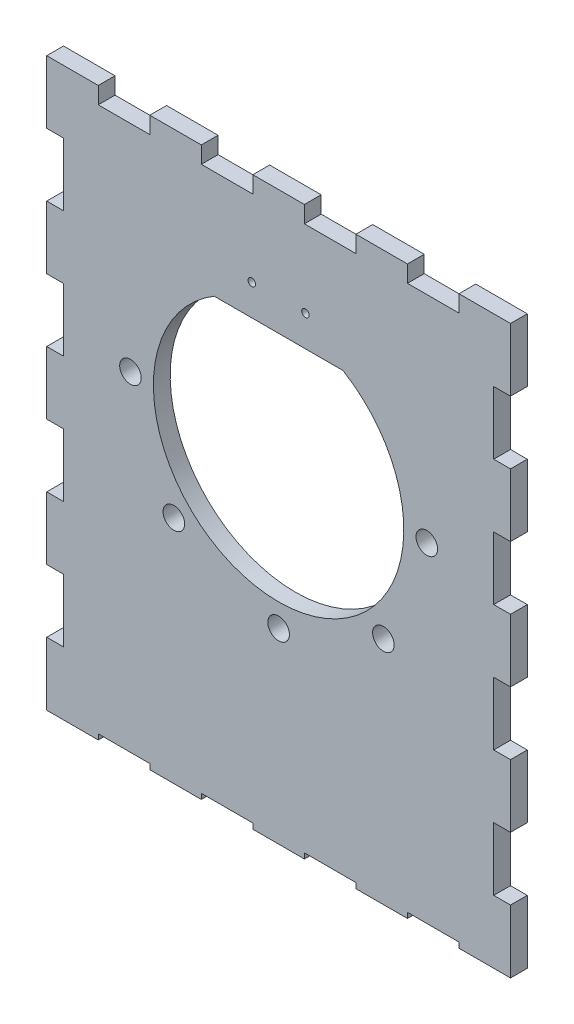
SolidWorks part; units mm, degrees
ref_plane "Front Plane" through (0, 0, 0) normal (0, 0, 1) x (1, 0, 0)
ref_plane "Top Plane" through (0, 0, 0) normal (0, 1, 0) x (1, 0, 0)
ref_plane "Right Plane" through (0, 0, 0) normal (1, 0, 0) x (0, 0, -1)
sketch "Sketch1" plane through (0, 0, 0) normal (0, 0, 1) x (1, 0, 0)
  line L0 (0, 0) -> (0, 68.58) construction
  line L1 (-68.58, -99.06) -> (68.58, -99.06)
  line L2 (-68.58, -99.06) -> (-68.58, 68.58)
  line L3 (-68.58, 68.58) -> (68.58, 68.58)
  line L4 (68.58, -99.06) -> (68.58, 68.58)
  point P0 (0, 0)
  dimension "D1" = 68.58
  dimension "D2" = 137.16
  dimension "D3" = 167.64
extrude "Boss-Extrude1" add sketch "Sketch1" along normal blind 4.9609
sketch "Sketch2" plane through (0, 0, 4.9609) normal (0, 0, 1) x (1, 0, 0)
  line L0 (-19.05, 31.75) -> (19.05, 31.75) construction
  line L1 (0, 31.75) -> (0, 0) construction
  line L2 (-19.05, 31.75) -> (19.05, 31.75)
  circle A0 centre (0, 0) radius 37.0265 construction
  arc A1 (-19.05, 31.75) -> (19.05, 31.75) centre (0, 0) ccw
  dimension "D1" = 38.1
  dimension "D2" = 31.75
extrude "Cut-Extrude1" cut sketch "Sketch2" against normal through all
sketch "Sketch4" plane through (0, 0, 4.9609) normal (0, 0, 1) x (1, 0, 0)
  line L0 (-43.815, 0) -> (43.815, 0) construction
  line L1 (0, 0) -> (-30.9819, -30.9819) construction
  line L2 (0, 0) -> (0, -43.815) construction
  line L3 (0, 0) -> (30.9819, -30.9819) construction
  circle A0 centre (0, 0) radius 43.815 construction
  circle A1 centre (-43.815, 0) radius 3.1877
  circle A2 centre (-30.9819, -30.9819) radius 3.1877
  circle A3 centre (0, -43.815) radius 3.1877
  circle A4 centre (30.9819, -30.9819) radius 3.1877
  circle A5 centre (43.815, 0) radius 3.1877
  point P6 (0, 0)
  dimension "D1" = 87.63
  dimension "D4" = 6.3754
  dimension "D2" = 45
  dimension "D3" = 45
extrude "Cut-Extrude2" cut sketch "Sketch4" against normal through all
sketch "Sketch6" plane through (0, 0, 4.9609) normal (0, 0, 1) x (1, 0, 0)
  line L20 (-68.58, 68.58) -> (-68.58, 49.9618) construction
  line L21 (-68.58, 68.58) -> (-68.58, -99.06) construction
  line L22 (-68.58, 12.7254) -> (-68.58, -5.8928)
  line L23 (-68.58, 49.9618) -> (-63.6165, 49.9618)
  line L24 (-68.58, 49.9618) -> (-68.58, 31.3436)
  line L25 (-68.58, 31.3436) -> (-63.6165, 31.3436)
  line L26 (-63.6165, 49.9618) -> (-63.6165, 31.3436)
  line L27 (-68.58, 12.7254) -> (-63.6165, 12.7254)
  line L28 (-63.6165, 12.7254) -> (-63.6165, -5.8928)
  line L29 (-68.58, -5.8928) -> (-63.6165, -5.8928)
  line L30 (-68.58, -24.511) -> (-68.58, -43.1292)
  line L31 (-68.58, -24.511) -> (-63.6165, -24.511)
  line L32 (-63.6165, -24.511) -> (-63.6165, -43.1292)
  line L33 (-68.58, -43.1292) -> (-63.6165, -43.1292)
  line L34 (-68.58, -61.7474) -> (-68.58, -80.3656)
  line L35 (-68.58, -61.7474) -> (-63.6165, -61.7474)
  line L36 (-63.6165, -61.7474) -> (-63.6165, -80.3656)
  line L37 (-68.58, -80.3656) -> (-63.6165, -80.3656)
  line L38 (-68.58, 68.58) -> (-53.34, 68.58) construction
  line L39 (-63.6165, 31.3436) -> (-63.6165, 12.7254) construction
  line L60 (68.58, 68.58) -> (-68.58, 68.58) construction
  line L61 (68.58, 68.58) -> (68.58, 49.9542) construction
  line L62 (68.58, -99.06) -> (68.58, 68.58) construction
  line L63 (68.58, 12.7178) -> (68.58, -5.9004)
  line L64 (68.58, 49.9542) -> (63.6165, 49.9542)
  line L65 (68.58, 49.9542) -> (68.58, 31.336)
  line L66 (68.58, 31.336) -> (63.6165, 31.336)
  line L67 (63.6165, 49.9542) -> (63.6165, 31.336)
  line L68 (68.58, 12.7178) -> (63.6165, 12.7178)
  line L69 (63.6165, 12.7178) -> (63.6165, -5.9004)
  line L70 (68.58, -5.9004) -> (63.6165, -5.9004)
  line L71 (68.58, -24.5186) -> (68.58, -43.1368)
  line L72 (68.58, -24.5186) -> (63.6165, -24.5186)
  line L73 (63.6165, -24.5186) -> (63.6165, -43.1368)
  line L74 (68.58, -43.1368) -> (63.6165, -43.1368)
  line L75 (68.58, -61.755) -> (68.58, -80.3732)
  line L76 (68.58, -61.755) -> (63.6165, -61.755)
  line L77 (63.6165, -61.755) -> (63.6165, -80.3732)
  line L78 (68.58, -80.3732) -> (63.6165, -80.3732)
  line L79 (63.6165, 31.336) -> (63.6165, 12.7178) construction
  line L80 (-22.86, 68.58) -> (-22.86, 63.6165)
  line L81 (-53.34, 68.58) -> (-38.1, 68.58)
  line L82 (-53.34, 68.58) -> (-53.34, 63.6165)
  line L83 (-53.34, 63.6165) -> (-38.1, 63.6165)
  line L84 (-38.1, 68.58) -> (-38.1, 63.6165)
  line L85 (-22.86, 68.58) -> (-7.62, 68.58)
  line L86 (-7.62, 68.58) -> (-7.62, 63.6165)
  line L87 (-22.86, 63.6165) -> (-7.62, 63.6165)
  line L88 (7.62, 68.58) -> (7.62, 63.6165)
  line L89 (7.62, 68.58) -> (22.86, 68.58)
  line L90 (22.86, 68.58) -> (22.86, 63.6165)
  line L91 (7.62, 63.6165) -> (22.86, 63.6165)
  line L92 (38.1, 68.58) -> (38.1, 63.6165)
  line L93 (38.1, 68.58) -> (53.34, 68.58)
  line L94 (53.34, 68.58) -> (53.34, 63.6165)
  line L95 (38.1, 63.6165) -> (53.34, 63.6165)
  line L96 (-38.1, 68.58) -> (-22.86, 68.58) construction
  line L97 (-68.58, -99.06) -> (-53.34, -99.06) construction
  line L98 (-68.58, -99.06) -> (68.58, -99.06) construction
  line L99 (-22.86, -99.06) -> (-22.86, -97.4725)
  line L100 (-53.34, -99.06) -> (-38.1, -99.06)
  line L101 (-53.34, -99.06) -> (-53.34, -97.4725)
  line L102 (-53.34, -97.4725) -> (-38.1, -97.4725)
  line L103 (-38.1, -99.06) -> (-38.1, -97.4725)
  line L104 (-22.86, -99.06) -> (-7.62, -99.06)
  line L105 (-7.62, -99.06) -> (-7.62, -97.4725)
  line L106 (-22.86, -97.4725) -> (-7.62, -97.4725)
  line L107 (7.62, -99.06) -> (7.62, -97.4725)
  line L108 (7.62, -99.06) -> (22.86, -99.06)
  line L109 (22.86, -99.06) -> (22.86, -97.4725)
  line L110 (7.62, -97.4725) -> (22.86, -97.4725)
  line L111 (38.1, -99.06) -> (38.1, -97.4725)
  line L112 (38.1, -99.06) -> (53.34, -99.06)
  line L113 (53.34, -99.06) -> (53.34, -97.4725)
  line L114 (38.1, -97.4725) -> (53.34, -97.4725)
  line L115 (-38.1, -97.4725) -> (-22.86, -97.4725) construction
  line L116 (-38.1, 63.6165) -> (-22.86, 63.6165) construction
  dimension "D2" = 15.24
  dimension "D4" = 18.6182
  dimension "D5" = 15.24
  dimension "D6" = 15.24
  dimension "D10" = 4
  dimension "D13" = 15.24
  dimension "D15" = 18.6182
  dimension "D16" = 4.9635
  dimension "D18" = 18.6182
  dimension "D3" = 1.5875
  dimension "D12" = 18.6258
  dimension "D7" = 4
  dimension "D17" = 4
  dimension "D20" = 4
extrude "Cut-Extrude5" cut sketch "Sketch6" against normal through all
sketch "Sketch7" plane through (0, 0, 4.9609) normal (0, 0, 1) x (1, 0, 0)
  line L0 (19.05, 31.75) -> (-19.05, 31.75) construction
  line L1 (19.05, 31.75) -> (-19.05, 31.75) construction
  line L2 (0, 31.75) -> (0, 40.8775) construction
  line L3 (-7.9375, 40.8775) -> (7.9375, 40.8775) construction
  line L68 (-63.6165, 49.9618) -> (-63.6165, 31.3436)
  line L69 (-63.6165, 31.3436) -> (-68.58, 31.3436)
  line L70 (-68.58, 31.3436) -> (-68.58, 12.7254)
  line L71 (-68.58, 12.7254) -> (-63.6165, 12.7254)
  line L72 (-63.6165, 12.7254) -> (-63.6165, -5.8928)
  line L73 (-63.6165, -5.8928) -> (-68.58, -5.8928)
  line L74 (-68.58, -5.8928) -> (-68.58, -24.511)
  line L75 (-68.58, -24.511) -> (-63.6165, -24.511)
  line L76 (-63.6165, -24.511) -> (-63.6165, -43.1292)
  line L77 (-63.6165, -43.1292) -> (-68.58, -43.1292)
  line L78 (-68.58, -43.1292) -> (-68.58, -61.7474)
  line L79 (-68.58, -61.7474) -> (-63.6165, -61.7474)
  line L80 (-63.6165, -61.7474) -> (-63.6165, -80.3656)
  line L81 (-63.6165, -80.3656) -> (-68.58, -80.3656)
  line L82 (-68.58, -80.3656) -> (-68.58, -99.06)
  line L83 (-68.58, -99.06) -> (-53.34, -99.06)
  line L84 (-53.34, -99.06) -> (-53.34, -97.4725)
  line L85 (-53.34, -97.4725) -> (-38.1, -97.4725)
  line L86 (-38.1, -97.4725) -> (-38.1, -99.06)
  line L87 (-38.1, -99.06) -> (-22.86, -99.06)
  line L88 (-22.86, -99.06) -> (-22.86, -97.4725)
  line L89 (-22.86, -97.4725) -> (-7.62, -97.4725)
  line L90 (-7.62, -97.4725) -> (-7.62, -99.06)
  line L91 (-7.62, -99.06) -> (7.62, -99.06)
  line L92 (7.62, -99.06) -> (7.62, -97.4725)
  line L93 (7.62, -97.4725) -> (22.86, -97.4725)
  line L94 (22.86, -97.4725) -> (22.86, -99.06)
  line L95 (22.86, -99.06) -> (38.1, -99.06)
  line L96 (38.1, -99.06) -> (38.1, -97.4725)
  line L97 (38.1, -97.4725) -> (53.34, -97.4725)
  line L98 (53.34, -97.4725) -> (53.34, -99.06)
  line L99 (53.34, -99.06) -> (68.58, -99.06)
  line L100 (68.58, -99.06) -> (68.58, -80.3732)
  line L101 (68.58, -80.3732) -> (63.6165, -80.3732)
  line L102 (63.6165, -80.3732) -> (63.6165, -61.755)
  line L103 (63.6165, -61.755) -> (68.58, -61.755)
  line L104 (68.58, -61.755) -> (68.58, -43.1368)
  line L105 (68.58, -43.1368) -> (63.6165, -43.1368)
  line L106 (63.6165, -43.1368) -> (63.6165, -24.5186)
  line L107 (63.6165, -24.5186) -> (68.58, -24.5186)
  line L108 (68.58, -24.5186) -> (68.58, -5.9004)
  line L109 (68.58, -5.9004) -> (63.6165, -5.9004)
  line L110 (63.6165, -5.9004) -> (63.6165, 12.7178)
  line L111 (63.6165, 12.7178) -> (68.58, 12.7178)
  line L112 (68.58, 12.7178) -> (68.58, 31.336)
  line L113 (68.58, 31.336) -> (63.6165, 31.336)
  line L114 (63.6165, 31.336) -> (63.6165, 49.9542)
  line L115 (63.6165, 49.9542) -> (68.58, 49.9542)
  line L116 (68.58, 49.9542) -> (68.58, 68.58)
  line L117 (68.58, 68.58) -> (53.34, 68.58)
  line L118 (53.34, 68.58) -> (53.34, 63.6165)
  line L119 (53.34, 63.6165) -> (38.1, 63.6165)
  line L120 (38.1, 63.6165) -> (38.1, 68.58)
  line L121 (38.1, 68.58) -> (22.86, 68.58)
  line L122 (22.86, 68.58) -> (22.86, 63.6165)
  line L123 (22.86, 63.6165) -> (7.62, 63.6165)
  line L124 (7.62, 63.6165) -> (7.62, 68.58)
  line L125 (7.62, 68.58) -> (-7.62, 68.58)
  line L126 (-7.62, 68.58) -> (-7.62, 63.6165)
  line L127 (-7.62, 63.6165) -> (-22.86, 63.6165)
  line L128 (-22.86, 63.6165) -> (-22.86, 68.58)
  line L129 (-22.86, 68.58) -> (-38.1, 68.58)
  line L130 (-38.1, 68.58) -> (-38.1, 63.6165)
  line L131 (-38.1, 63.6165) -> (-53.34, 63.6165)
  line L132 (-53.34, 63.6165) -> (-53.34, 68.58)
  line L133 (-53.34, 68.58) -> (-68.58, 68.58)
  line L134 (-68.58, 68.58) -> (-68.58, 49.9618)
  line L135 (-68.58, 49.9618) -> (-63.6165, 49.9618)
  line L136 (-63.6165, 49.9618) -> (-63.6165, 31.3436)
  line L137 (-63.6165, 31.3436) -> (-68.58, 31.3436)
  line L138 (-68.58, 31.3436) -> (-68.58, 12.7254)
  line L139 (-68.58, 12.7254) -> (-63.6165, 12.7254)
  line L140 (-63.6165, 12.7254) -> (-63.6165, -5.8928)
  line L141 (-63.6165, -5.8928) -> (-68.58, -5.8928)
  line L142 (-68.58, -5.8928) -> (-68.58, -24.511)
  line L143 (-68.58, -24.511) -> (-63.6165, -24.511)
  line L144 (-63.6165, -24.511) -> (-63.6165, -43.1292)
  line L145 (-63.6165, -43.1292) -> (-68.58, -43.1292)
  line L146 (-68.58, -43.1292) -> (-68.58, -61.7474)
  line L147 (-68.58, -61.7474) -> (-63.6165, -61.7474)
  line L148 (-63.6165, -61.7474) -> (-63.6165, -80.3656)
  line L149 (-63.6165, -80.3656) -> (-68.58, -80.3656)
  line L150 (-68.58, -80.3656) -> (-68.58, -99.06)
  line L151 (-68.58, -99.06) -> (-53.34, -99.06)
  line L152 (-53.34, -99.06) -> (-53.34, -97.4725)
  line L153 (-53.34, -97.4725) -> (-38.1, -97.4725)
  line L154 (-38.1, -97.4725) -> (-38.1, -99.06)
  line L155 (-38.1, -99.06) -> (-22.86, -99.06)
  line L156 (-22.86, -99.06) -> (-22.86, -97.4725)
  line L157 (-22.86, -97.4725) -> (-7.62, -97.4725)
  line L158 (-7.62, -97.4725) -> (-7.62, -99.06)
  line L159 (-7.62, -99.06) -> (7.62, -99.06)
  line L160 (7.62, -99.06) -> (7.62, -97.4725)
  line L161 (7.62, -97.4725) -> (22.86, -97.4725)
  line L162 (22.86, -97.4725) -> (22.86, -99.06)
  line L163 (22.86, -99.06) -> (38.1, -99.06)
  line L164 (38.1, -99.06) -> (38.1, -97.4725)
  line L165 (38.1, -97.4725) -> (53.34, -97.4725)
  line L166 (53.34, -97.4725) -> (53.34, -99.06)
  line L167 (53.34, -99.06) -> (68.58, -99.06)
  line L168 (68.58, -99.06) -> (68.58, -80.3732)
  line L169 (68.58, -80.3732) -> (63.6165, -80.3732)
  line L170 (63.6165, -80.3732) -> (63.6165, -61.755)
  line L171 (63.6165, -61.755) -> (68.58, -61.755)
  line L172 (68.58, -61.755) -> (68.58, -43.1368)
  line L173 (68.58, -43.1368) -> (63.6165, -43.1368)
  line L174 (63.6165, -43.1368) -> (63.6165, -24.5186)
  line L175 (63.6165, -24.5186) -> (68.58, -24.5186)
  line L176 (68.58, -24.5186) -> (68.58, -5.9004)
  line L177 (68.58, -5.9004) -> (63.6165, -5.9004)
  line L178 (63.6165, -5.9004) -> (63.6165, 12.7178)
  line L179 (63.6165, 12.7178) -> (68.58, 12.7178)
  line L180 (68.58, 12.7178) -> (68.58, 31.336)
  line L181 (68.58, 31.336) -> (63.6165, 31.336)
  line L182 (63.6165, 31.336) -> (63.6165, 49.9542)
  line L183 (63.6165, 49.9542) -> (68.58, 49.9542)
  line L184 (68.58, 49.9542) -> (68.58, 68.58)
  line L185 (68.58, 68.58) -> (53.34, 68.58)
  line L186 (53.34, 68.58) -> (53.34, 63.6165)
  line L187 (53.34, 63.6165) -> (38.1, 63.6165)
  line L188 (38.1, 63.6165) -> (38.1, 68.58)
  line L189 (38.1, 68.58) -> (22.86, 68.58)
  line L190 (22.86, 68.58) -> (22.86, 63.6165)
  line L191 (22.86, 63.6165) -> (7.62, 63.6165)
  line L192 (7.62, 63.6165) -> (7.62, 68.58)
  line L193 (7.62, 68.58) -> (-7.62, 68.58)
  line L194 (-7.62, 68.58) -> (-7.62, 63.6165)
  line L195 (-7.62, 63.6165) -> (-22.86, 63.6165)
  line L196 (-22.86, 63.6165) -> (-22.86, 68.58)
  line L197 (-22.86, 68.58) -> (-38.1, 68.58)
  line L198 (-38.1, 68.58) -> (-38.1, 63.6165)
  line L199 (-38.1, 63.6165) -> (-53.34, 63.6165)
  line L200 (-53.34, 63.6165) -> (-53.34, 68.58)
  line L201 (-53.34, 68.58) -> (-68.58, 68.58)
  line L202 (-68.58, 68.58) -> (-68.58, 49.9618)
  line L203 (-68.58, 49.9618) -> (-63.6165, 49.9618)
  circle A0 centre (-7.9375, 40.8775) radius 1.1049
  circle A1 centre (7.9375, 40.8775) radius 1.1049
  point P16 (0, 40.8775)
  dimension "D4" = 2.2098
  dimension "D2" = 9.1275
  dimension "D3" = 15.875
  dimension "D1" = 0
extrude "Cut-Extrude6" cut sketch "Sketch7" against normal through all flip side to cut
